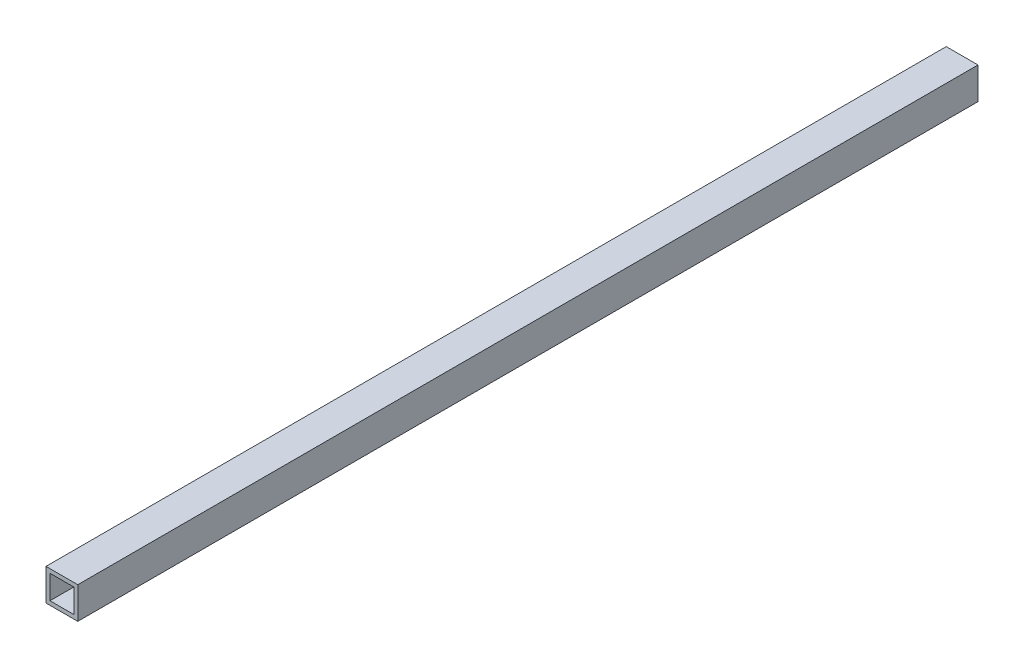
SolidWorks part; units mm, degrees
ref_plane "Front Plane" through (0, 0, 0) normal (0, 0, 1) x (1, 0, 0)
ref_plane "Top Plane" through (0, 0, 0) normal (0, 1, 0) x (1, 0, 0)
ref_plane "Right Plane" through (0, 0, 0) normal (1, 0, 0) x (0, 0, -1)
sketch "Sketch1" plane through (0, 0, 0) normal (0, 0, 1) x (1, 0, 0)
  line L0 (0, 12) -> (12, 0) construction
  line L1 (0, 0) -> (12, 0)
  line L2 (0, 0) -> (0, 12)
  line L3 (0, 12) -> (12, 12)
  line L4 (12, 0) -> (12, 12)
  line L6 (1.5, 1.5) -> (10.5, 1.5)
  line L7 (1.5, 1.5) -> (1.5, 10.5)
  line L8 (1.5, 10.5) -> (10.5, 10.5)
  line L9 (10.5, 1.5) -> (10.5, 10.5)
  line L10 (1.5, 1.5) -> (10.5, 10.5) construction
  line L11 (1.5, 10.5) -> (10.5, 1.5) construction
  point P5 (6, 6)
  dimension "D1" = 12
  dimension "D2" = 12
  dimension "D3" = 9
extrude "Boss-Extrude1" add sketch "Sketch1" along normal blind 340
